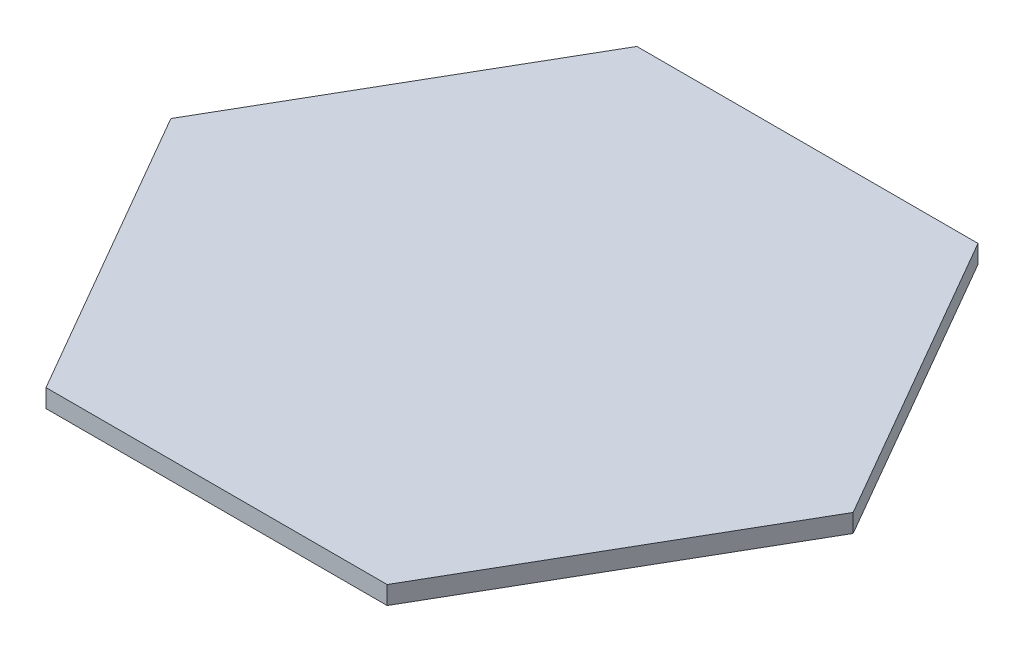
SolidWorks part; units mm, degrees
material "1060 Alloy"
ref_plane "Front Plane" through (0, 0, 0) normal (0, 0, 1) x (1, 0, 0)
ref_plane "Top Plane" through (0, 0, 0) normal (0, 1, 0) x (1, 0, 0)
ref_plane "Right Plane" through (0, 0, 0) normal (1, 0, 0) x (0, 0, -1)
sketch "Sketch1" plane through (0, 0, 0) normal (0, 1, 0) x (1, 0, 0)
  line L0 (59.4397, 0) -> (29.7198, 51.4763)
  line L7 (29.7198, 51.4763) -> (-29.7198, 51.4763)
  line L8 (-29.7198, 51.4763) -> (-59.4397, 0)
  line L9 (-59.4397, 0) -> (-29.7198, -51.4763)
  line L10 (-29.7198, -51.4763) -> (29.7198, -51.4763)
  line L11 (29.7198, -51.4763) -> (59.4397, 0)
extrude "Boss-Extrude1" add sketch "Sketch1" along normal blind 3.175
